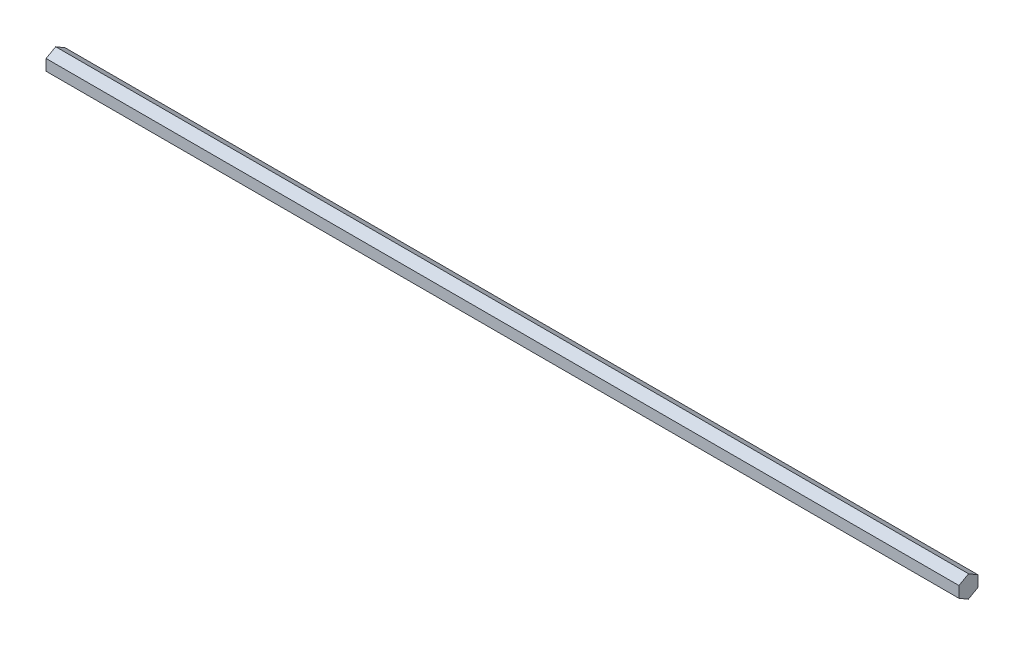
SolidWorks part; units mm, degrees
material "Cast Alloy Steel"
ref_plane "Front Plane" through (0, 0, 0) normal (0, 0, 1) x (1, 0, 0)
ref_plane "Top Plane" through (0, 0, 0) normal (0, 1, 0) x (1, 0, 0)
ref_plane "Right Plane" through (0, 0, 0) normal (1, 0, 0) x (0, 0, -1)
sketch "Sketch1" plane through (0, 0, 0) normal (1, 0, 0) x (0, 0, -1)
  line L1 (6.3871, 3.6012) -> (0.0748, 7.332)
  line L2 (0.0748, 7.332) -> (-6.3123, 3.7308)
  line L3 (-6.3123, 3.7308) -> (-6.3871, -3.6012)
  line L4 (-6.3871, -3.6012) -> (-0.0748, -7.332)
  line L5 (-0.0748, -7.332) -> (6.3123, -3.7308)
  line L6 (6.3123, -3.7308) -> (6.3871, 3.6012)
  circle A0 centre (0, 0) radius 6.35 construction
  dimension "D1" = 12.7
extrude "Boss-Extrude1" add sketch "Sketch1" along normal blind 609.6
